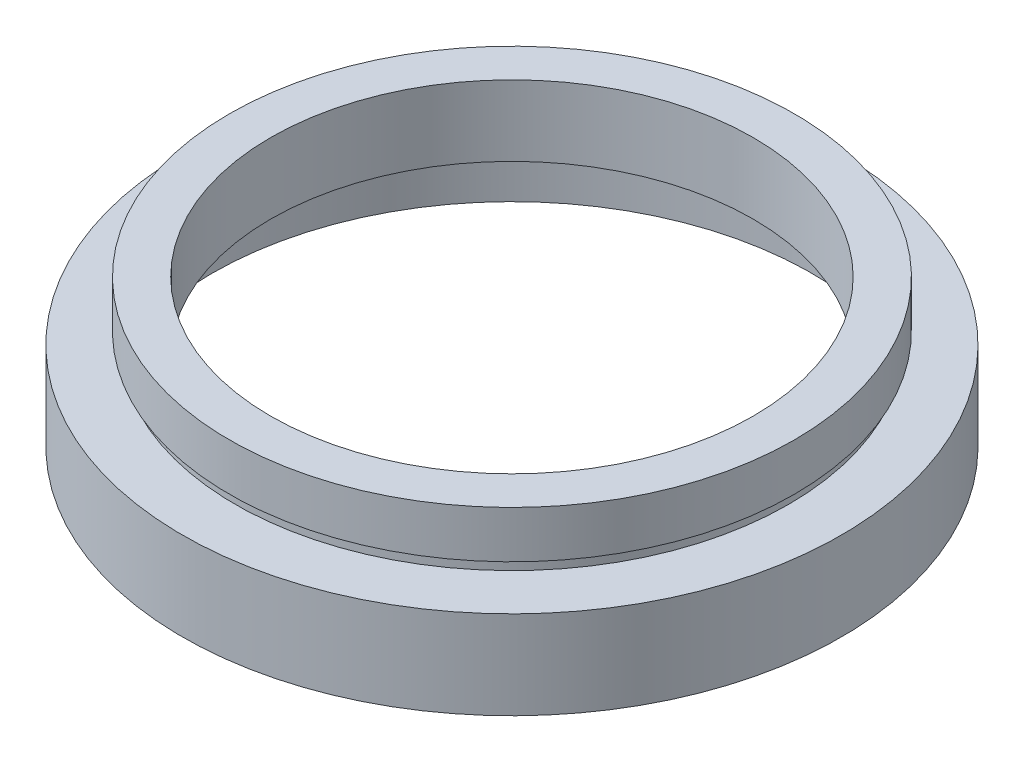
SolidWorks part; units mm, degrees
ref_plane "前视基准面" through (0, 0, 0) normal (0, 0, 1) x (1, 0, 0)
ref_plane "上视基准面" through (0, 0, 0) normal (0, 1, 0) x (1, 0, 0)
ref_plane "右视基准面" through (0, 0, 0) normal (1, 0, 0) x (0, 0, -1)
sketch "草图1" plane through (0, 0, 0) normal (0, 0, 1) x (1, 0, 0)
  line L0 (0, 16.886) -> (0, -24.4878) construction
  line L1 (25.5, 0) -> (25.5, 5.5)
  line L2 (20.5, 6.5) -> (26.1, 6.5)
  line L3 (20.5, 6.5) -> (20.5, 12.5)
  line L4 (20.5, 12.5) -> (24, 12.5)
  line L5 (24, 12.5) -> (24, 8.5)
  line L6 (24, 8.5) -> (23.5, 8.5)
  line L7 (23.5, 8.5) -> (23.5, 7.5)
  line L8 (23.5, 7.5) -> (28, 7.5)
  line L9 (28, 7.5) -> (28, 0)
  line L10 (28, 0) -> (25.5, 0)
  line L11 (25.5, 5.5) -> (26.1, 5.5)
  line L12 (26.1, 5.5) -> (26.1, 6.5)
  line L13 (0, 0) -> (3.4668, 0) construction
  point P4 (26.75, 0)
  dimension "D1" = 20.5
  dimension "D2" = 24
  dimension "D3" = 23.5
  dimension "D4" = 25.5
  dimension "D5" = 26.1
  dimension "D6" = 28
  dimension "D7" = 12.5
  dimension "D8" = 7.5
  dimension "D9" = 1
  dimension "D10" = 5.5
  dimension "D11" = 1
revolve "旋转1" add sketch "草图1" angle 360 about L0
cosmetic thread "装饰螺纹线1" parameters "D1"=4, "D2"=47
cosmetic thread "装饰螺纹线2" parameters "D1"=4, "D2"=42
cosmetic thread "装饰螺纹线3" parameters "D1"=4, "D2"=52
